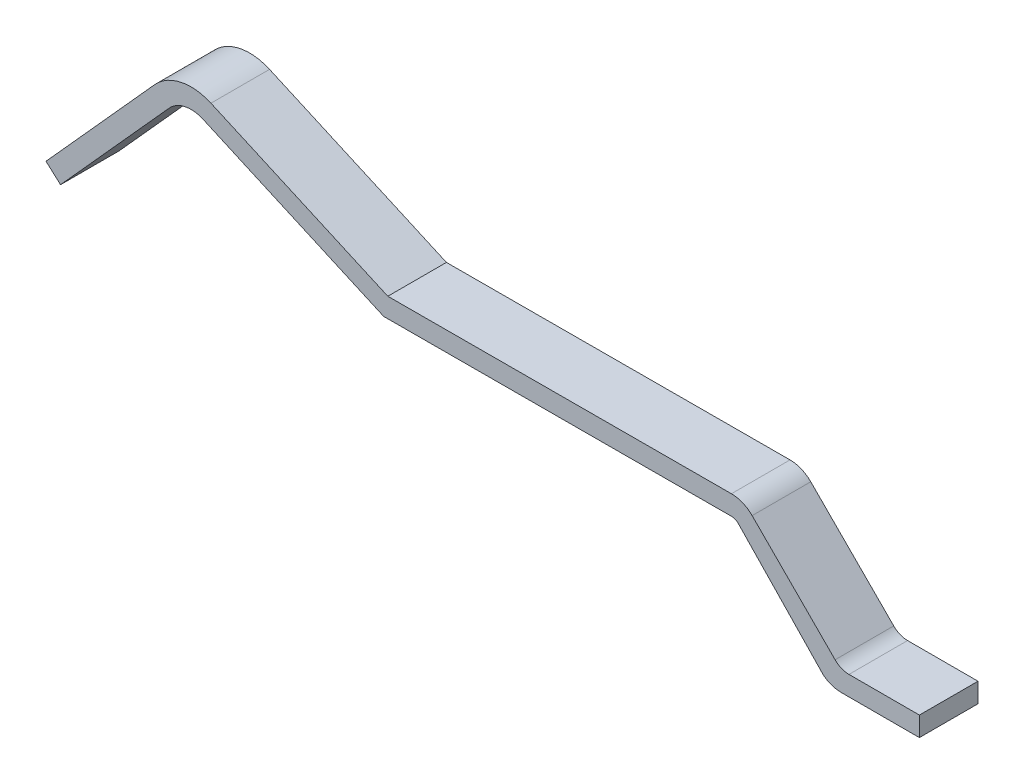
SolidWorks part; units mm, degrees
ref_plane "Plano frontal" through (0, 0, 0) normal (0, 0, 1) x (1, 0, 0)
ref_plane "Plano superior" through (0, 0, 0) normal (0, 1, 0) x (1, 0, 0)
ref_plane "Plano direito" through (0, 0, 0) normal (1, 0, 0) x (0, 0, -1)
sketch "Esboço1" plane through (0, 0, 0) normal (0, 0, 1) x (1, 0, 0)
  line L0 (17.8918, 0.1979) -> (17.8918, -0.0021)
  line L1 (17.8918, -0.0021) -> (17.0918, -0.0021)
  line L3 (16.9118, 0.0579) -> (16.0382, 0.9688)
  line L5 (15.9675, 0.998) -> (12.4075, 0.99)
  line L8 (12.4075, 0.99) -> (10.558, 1.8135)
  line L11 (10.213, 1.7401) -> (9.0995, 0.5035)
  line L12 (9.0995, 0.5035) -> (8.9509, 0.6373)
  line L13 (8.9509, 0.6373) -> (10.0644, 1.874)
  line L17 (10.6393, 1.9962) -> (12.45, 1.19)
  line L19 (12.45, 1.19) -> (15.9675, 1.1979)
  line L21 (16.1796, 1.1101) -> (17.029, 0.2568)
  line L22 (17.1707, 0.1979) -> (17.8918, 0.1979)
  arc A2 (17.029, 0.2568) -> (17.1707, 0.1979) centre (17.1707, 0.3979) ccw
  arc A3 (17.0918, -0.0021) -> (16.9118, 0.0579) centre (17.0918, 0.2979) cw
  arc A4 (15.9675, 0.998) -> (16.0382, 0.9688) centre (15.9677, 0.8986) cw
  arc A5 (16.1796, 1.1101) -> (15.9675, 1.1979) centre (15.9682, 0.8996) ccw
  arc A6 (10.558, 1.8135) -> (10.213, 1.7401) centre (10.436, 1.5394) ccw
  arc A7 (10.6393, 1.9962) -> (10.0644, 1.874) centre (10.436, 1.5394) ccw
  dimension "D1" = 0.2
  dimension "D11" = 0.0995
  dimension "D12" = 0.2984
  dimension "D13" = 0.3
  dimension "D2" = 0.8736
  dimension "D3" = 0.8
  dimension "D4" = 0.8494
  dimension "D5" = 0.721
  dimension "D6" = 3.56
  dimension "D7" = 0.0707
  dimension "D8" = 0.18
  dimension "D9" = 0.2121
  dimension "D10" = 0.1417
  dimension "D14" = 0.1999
extrude "Ressalto-extrusão1" add sketch "Esboço1" along normal mid plane 0.6
